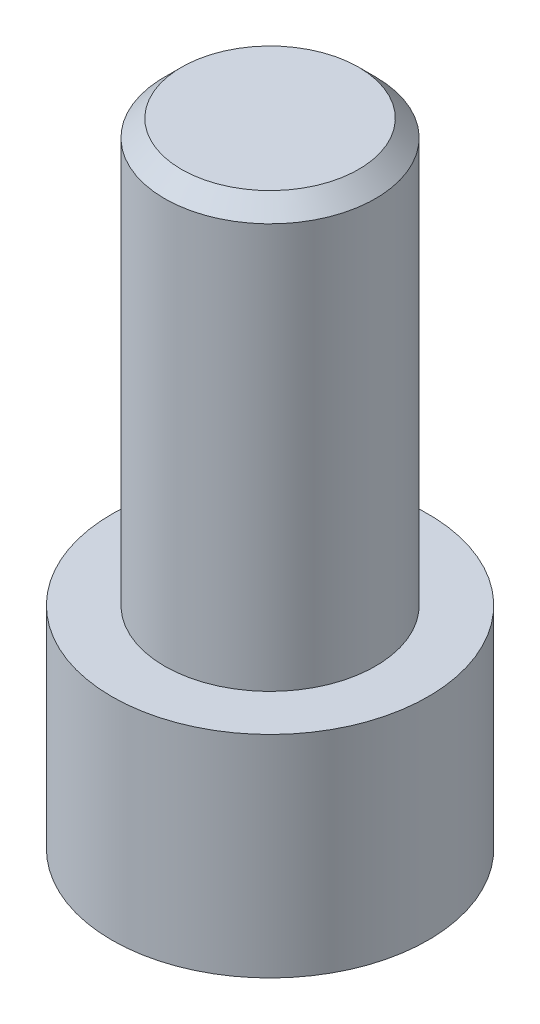
SolidWorks part; units mm, degrees
material "1023 Carbon Steel Sheet (SS)"
ref_plane "Front Plane" through (0, 0, 0) normal (0, 0, 1) x (1, 0, 0)
ref_plane "Top Plane" through (0, 0, 0) normal (0, 1, 0) x (1, 0, 0)
ref_plane "Right Plane" through (0, 0, 0) normal (1, 0, 0) x (0, 0, -1)
sketch "Sketch1" plane through (0, 0, 0) normal (0, 0, 1) x (1, 0, 0)
  line L0 (0, 19.05) -> (0, -21.565) construction
  line L1 (0, 0) -> (0, 19.05)
  line L2 (0, 19.05) -> (3.175, 19.05)
  line L3 (3.175, 19.05) -> (3.175, 6.35)
  line L4 (3.175, 6.35) -> (4.7625, 6.35)
  line L5 (4.7625, 6.35) -> (4.7625, 0)
  line L6 (4.7625, 0) -> (0, 0)
  dimension "D1" = 12.7
  dimension "D2" = 6.35
  dimension "D3" = 4.7625
  dimension "D4" = 3.175
revolve "Revolve1" add sketch "Sketch1" angle 360 about L0
chamfer "Chamfer1" distance 0.508 angle 45 1 edges at (0, 19.05, 3.175)
sketch "Sketch2" plane through (0, 0, 0) normal (0, -1, 0) x (1, 0, 0)
  line L1 (1.7219, -1.8672) -> (2.478, 0.5576)
  line L2 (2.478, 0.5576) -> (0.7561, 2.4249)
  line L3 (0.7561, 2.4249) -> (-1.7219, 1.8672)
  line L4 (-1.7219, 1.8672) -> (-2.478, -0.5576)
  line L5 (-2.478, -0.5576) -> (-0.7561, -2.4249)
  line L6 (-0.7561, -2.4249) -> (1.7219, -1.8672)
  circle A0 centre (0, 0) radius 2.1997 construction
  dimension "D1" = 5.08
extrude "Cut-Extrude1" cut sketch "Sketch2" against normal blind 3.81
